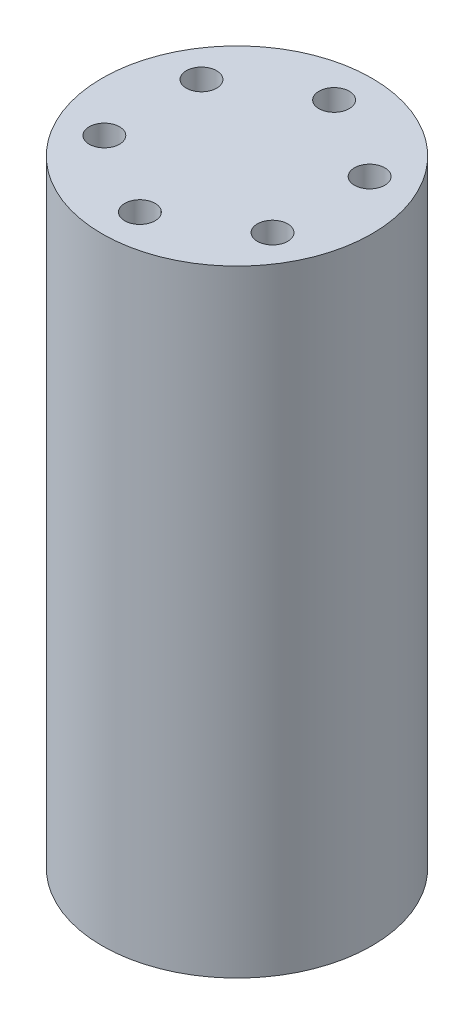
SolidWorks part; units mm, degrees
ref_plane "Front" through (0, 0, 0) normal (0, 0, 1) x (1, 0, 0)
ref_plane "Top" through (0, 0, 0) normal (0, 1, 0) x (1, 0, 0)
ref_plane "Right" through (0, 0, 0) normal (1, 0, 0) x (0, 0, -1)
sketch "Sketch1" plane through (0, 0, 0) normal (0, 1, 0) x (1, 0, 0)
  circle A0 centre (0, 0) radius 11.1125
  dimension "D1" = 22.225
extrude "Boss-Extrude1" add sketch "Sketch1" along normal blind 50.8
sketch "Sketch4" plane through (0, 50.8, 0) normal (0, 1, 0) x (1, 0, 0)
  circle A0 centre (0, 0) radius 8 construction
  point P0 (0, 8)
  point P10 (6.9282, 4)
  point P11 (6.9282, -4)
  point P12 (0, -8)
  point P13 (-6.9282, -4)
  point P14 (-6.9282, 4)
  point P16 (8.0553, 1.8424)
  point P17 (0, 0)
  point P18 (0, 0)
  dimension "D1" = 16
  dimension "D2" = 6
hole_wizard "M3x0.5 Tapped Hole1" positions "Sketch4" profile "Sketch5" tap size "M3x0.5" standard "ANSI Metric" end condition through all
sketch "Sketch5" plane through (0, 50.8, -8) normal (1, 0, 0) x (0, 0, 1)
  line L0 (0, 0) -> (0, 50.8)
  line L1 (0, 50.8) -> (1.25, 50.8)
  line L2 (1.25, 50.8) -> (1.25, 0)
  line L5 (1.25, 0) -> (0, 0)
  line L11 (0, -6.35) -> (0, 107.95) construction
  dimension "Thru Tap Drill Dia." = 2.5
  dimension "Thru Tap Drill Depth" = 50.8
cosmetic thread "Hole Thread1"
cosmetic thread "Hole Thread2"
cosmetic thread "Hole Thread3"
cosmetic thread "Hole Thread4"
cosmetic thread "Hole Thread5"
cosmetic thread "Hole Thread6"
